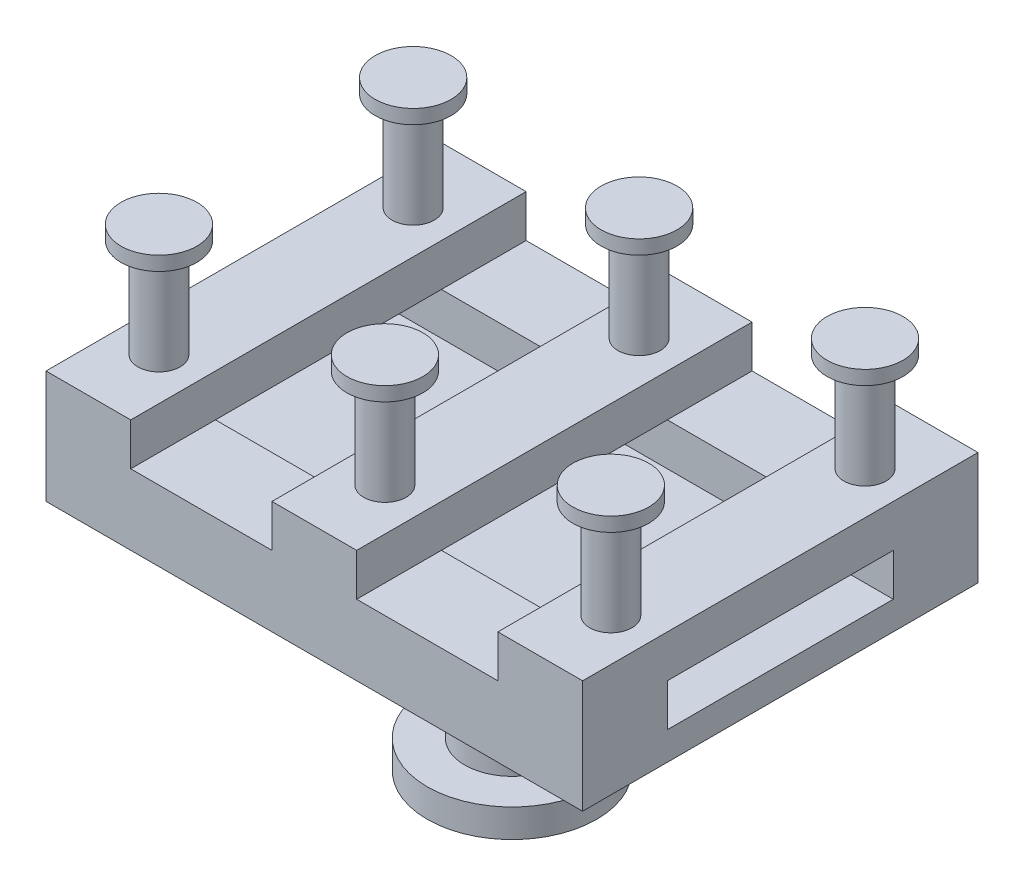
SolidWorks part; units mm, degrees
ref_plane "前视基准面" through (0, 0, 0) normal (0, 0, 1) x (1, 0, 0)
ref_plane "上视基准面" through (0, 0, 0) normal (0, 1, 0) x (1, 0, 0)
ref_plane "右视基准面" through (0, 0, 0) normal (1, 0, 0) x (0, 0, -1)
sketch "草图3" plane through (0, 0, 0) normal (0, 1, 0) x (1, 0, 0)
  circle A0 centre (0, 0) radius 60
  dimension "D1" = 120
extrude "凸台-拉伸1" add sketch "草图3" along normal blind 20
sketch "草图4" plane through (0, 20, 0) normal (0, 1, 0) x (1, 0, 0)
  circle A0 centre (0, 0) radius 33.4207
extrude "凸台-拉伸2" add sketch "草图4" along normal blind 110
sketch "草图7" plane through (0, 130, 0) normal (0, 1, 0) x (1, 0, 0)
  circle A0 centre (0, 0) radius 60
extrude "凸台-拉伸4" add sketch "草图7" along normal blind 10
sketch "草图9" plane through (0, 140, 0) normal (0, 1, 0) x (1, 0, 0)
  line L1 (-190, -140) -> (190, -140)
  line L2 (-190, -140) -> (-190, 140)
  line L3 (-190, 140) -> (190, 140)
  line L4 (190, -140) -> (190, 140)
  line L5 (-190, -140) -> (190, 140) construction
  line L6 (-190, 140) -> (190, -140) construction
  point P0 (0, 0)
  dimension "D1" = 380
  dimension "D2" = 280
extrude "凸台-拉伸5" add sketch "草图9" along normal blind 20
sketch "草图11" plane through (0, 160, 0) normal (0, 1, 0) x (1, 0, 0)
  line L0 (190, -140) -> (190, 140) construction
  line L1 (-190, 140) -> (190, 140)
  line L2 (-190, 140) -> (-190, 80)
  line L3 (-190, 80) -> (190, 80)
  line L4 (190, 140) -> (190, 80)
  line L5 (-190, 140) -> (-190, -140) construction
  line L6 (190, -140) -> (-190, -140)
  line L7 (190, -140) -> (190, -80)
  line L8 (190, -80) -> (-190, -80)
  line L9 (-190, -140) -> (-190, -80)
  dimension "D1" = 60
  dimension "D2" = 60
extrude "凸台-拉伸6" add sketch "草图11" along normal blind 30
sketch "草图13" plane through (0, 0, 140) normal (0, 0, 1) x (1, 0, 0)
  line L0 (-190, 190) -> (190, 190) construction
  line L1 (-190, 190) -> (-130, 190)
  line L2 (-190, 190) -> (-190, 220)
  line L3 (-190, 220) -> (-130, 220)
  line L4 (-130, 190) -> (-130, 220)
  line L5 (-30, 190) -> (30, 190)
  line L6 (-30, 190) -> (-30, 220)
  line L7 (-30, 220) -> (30, 220)
  line L8 (30, 190) -> (30, 220)
  line L10 (190, 190) -> (130, 190)
  line L11 (190, 190) -> (190, 220)
  line L12 (190, 220) -> (130, 220)
  line L13 (130, 190) -> (130, 220)
  dimension "D1" = 60
  dimension "D2" = 60
  dimension "D3" = 60
  dimension "D4" = 30
  dimension "D5" = 30
  dimension "D6" = 30
  dimension "D7" = 100
extrude "凸台-拉伸7" add sketch "草图13" against normal up to surface (280 mm away) up to face at (0, 165, -140)
sketch "草图14" plane through (0, 220, 0) normal (0, 1, 0) x (1, 0, 0)
  line L0 (-190, 140) -> (-190, -140) construction
  line L1 (-190, 140) -> (-130, 140) construction
  circle A0 centre (-160, 90) radius 15
  circle A1 centre (0, 90) radius 15
  circle A2 centre (160, 90) radius 15
  circle A6 centre (-160, -90) radius 15
  circle A7 centre (0, -90) radius 15
  circle A8 centre (160, -90) radius 15
  circle A9 centre (-160, 0) radius 15 [skipped]
  circle A10 centre (0, 0) radius 15 [skipped]
  circle A11 centre (160, 0) radius 15 [skipped]
  point P6 (-160, 140)
  dimension "D1" = 30
  dimension "D2" = 30
  dimension "D3" = 50
  dimension "D4" = 3
  dimension "D5" = 3
extrude "凸台-拉伸8" add sketch "草图14" along normal blind 70
sketch "草图16" plane through (0, 290, 0) normal (0, 1, 0) x (1, 0, 0)
  circle A0 centre (-160, 90) radius 26.8796
  circle A1 centre (0, 90) radius 26.8796
  circle A2 centre (160, 90) radius 26.8796
  circle A6 centre (-160, -90) radius 26.8796
  circle A7 centre (0, -90) radius 26.8796
  circle A8 centre (160, -90) radius 26.8796
  circle A9 centre (-160, 0) radius 26.8796 [skipped]
  circle A10 centre (0, 0) radius 26.8796 [skipped]
  circle A11 centre (160, 0) radius 26.8796 [skipped]
  dimension "D1" = 3
  dimension "D2" = 3
extrude "凸台-拉伸9" add sketch "草图16" along normal blind 10
